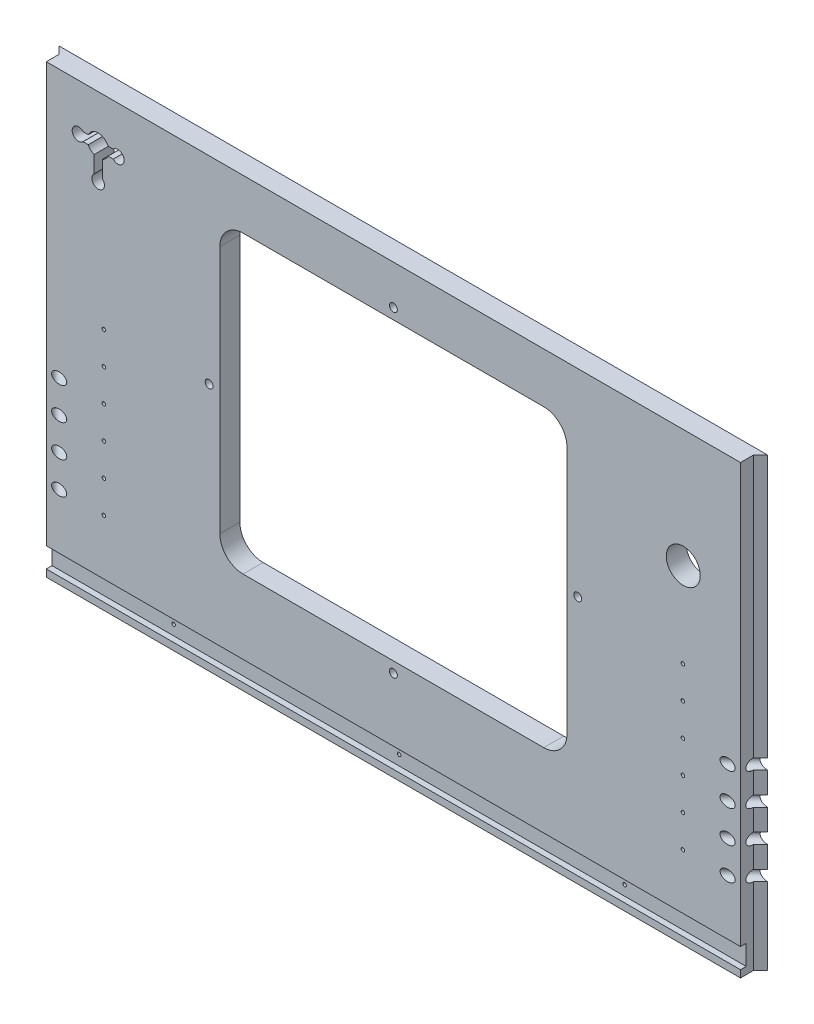
SolidWorks part; units mm, degrees
material "Maple"
ref_plane "Front Plane" through (0, 0, 0) normal (0, 0, 1) x (1, 0, 0)
ref_plane "Top Plane" through (0, 0, 0) normal (0, 1, 0) x (1, 0, 0)
ref_plane "Right Plane" through (0, 0, 0) normal (1, 0, 0) x (0, 0, -1)
sketch "Sketch1" plane through (0, 0, 0) normal (0, 0, 1) x (1, 0, 0)
  line L0 (8932.6508, -5243.5125) -> (10226.1458, -5243.5125)
  line L1 (9086.3208, -4722.0918) -> (10222.9708, -4853.7812)
  line L2 (8914.8708, -6342.0625) -> (10197.5708, -6342.0625)
  line L3 (8914.8708, -5808.6625) -> (10197.5708, -5808.6625)
  line L4 (8919.6333, -5253.0375) -> (10218.2083, -5253.0375)
  line L5 (9134.2633, -4656.1375) -> (9134.2633, -4638.3575)
  line L6 (9091.0833, -4638.3575) -> (9134.2633, -4638.3575)
  line L7 (9091.0833, -4567.2375) -> (9091.0833, -4638.3575)
  line L8 (9134.2633, -4656.1375) -> (9581.3033, -4656.1375)
  line L9 (9091.0833, -4567.2375) -> (9624.4833, -4567.2375)
  line L10 (9581.3033, -4656.1375) -> (9581.3033, -4638.3575)
  line L11 (9581.3033, -4638.3575) -> (9624.4833, -4638.3575)
  line L12 (9624.4833, -4567.2375) -> (9624.4833, -4638.3575)
  line L13 (8932.6508, -5225.7325) -> (9344.9775, -5225.7325)
  line L14 (8932.6508, -5256.2125) -> (8932.6508, -5243.5125)
  line L15 (8911.6958, -5256.2125) -> (8932.6508, -5256.2125)
  line L16 (8914.8708, -4722.0918) -> (9086.3208, -4722.0918)
  line L17 (8911.6958, -4715.5913) -> (8932.6508, -4715.5913)
  line L18 (8914.8708, -6342.0625) -> (8914.8708, -5808.6625)
  line L19 (12082.9917, -4722.0918) -> (10946.3417, -4853.7812)
  line L20 (12236.6617, -5243.5125) -> (10943.1667, -5243.5125)
  line L21 (10951.1042, -5253.0375) -> (12249.6792, -5253.0375)
  line L22 (10838.3917, -5656.2625) -> (11308.2917, -5656.2625)
  line L23 (10838.3917, -5719.7625) -> (11308.2917, -5719.7625)
  line L24 (10838.3917, -5742.5368) -> (11308.2917, -5742.5368)
  line L25 (10806.6417, -6342.0625) -> (11340.0417, -6342.0625)
  line L26 (10803.4667, -6335.7125) -> (11343.2167, -6335.7125)
  line L27 (10803.4667, -6317.9325) -> (11343.2167, -6317.9325)
  line L28 (10943.1667, -5225.7325) -> (11376.4483, -5225.7325)
  line L29 (11506.7292, -4754.5625) -> (10806.6417, -4827.5875)
  line L30 (11506.7292, -4567.2375) -> (11506.7292, -4754.5625)
  line L31 (10806.6417, -4567.2375) -> (10806.6417, -4827.5875)
  line L32 (10806.6417, -4567.2375) -> (11506.7292, -4567.2375)
  line L33 (10235.6708, -6329.3625) -> (10245.1958, -6329.3625)
  line L34 (10245.1958, -6329.3625) -> (10254.7208, -6278.5625)
  line L35 (10302.3458, -6329.3625) -> (10311.8708, -6278.5625)
  line L36 (10302.3458, -6329.3625) -> (10292.8208, -6329.3625)
  line L37 (10245.1958, -5821.3625) -> (10254.7208, -5872.1625)
  line L38 (10235.6708, -5821.3625) -> (10245.1958, -5821.3625)
  line L39 (10292.8208, -5821.3625) -> (10302.3458, -5821.3625)
  line L40 (10302.3458, -5821.3625) -> (10311.8708, -5872.1625)
  line L41 (10235.6708, -5821.3625) -> (10235.6708, -6329.3625)
  line L42 (10254.7208, -5872.1625) -> (10254.7208, -6278.5625)
  line L43 (10311.8708, -5872.1625) -> (10311.8708, -6278.5625)
  line L44 (10292.8208, -5821.3625) -> (10292.8208, -6329.3625)
  line L45 (8932.6508, -5225.7325) -> (8932.6508, -4715.5913)
  line L46 (8911.6958, -4715.5913) -> (8911.6958, -5256.2125)
  line L47 (8914.8708, -5248.275) -> (8914.8708, -4722.0918)
  line L48 (8919.6333, -5253.0375) -> (8914.8708, -5248.275)
  line L49 (8914.8708, -5145.0875) -> (8937.426, -5145.0875)
  line L50 (8914.8708, -5202.2375) -> (8937.426, -5202.2375)
  line L51 (10838.3917, -5656.2625) -> (10838.3917, -5719.7625)
  line L52 (10832.0417, -5736.1868) -> (10856.1717, -5736.1868)
  line L53 (10806.6417, -6342.0625) -> (10806.6417, -5818.7368)
  line L54 (10832.0417, -5649.9125) -> (10856.1717, -5649.9125)
  line L55 (10832.0417, -5726.1125) -> (10856.1717, -5726.1125)
  line L56 (10806.6417, -5818.7368) -> (10833.9015, -5818.7368)
  line L57 (10832.0417, -5806.0442) -> (10851.6815, -5806.0442)
  line L58 (10856.1717, -5801.5541) -> (10856.1717, -5736.1868)
  line L59 (10838.3917, -5814.2467) -> (10838.3917, -5742.5368)
  line L60 (10832.0417, -5806.0442) -> (10832.0417, -5736.1868)
  line L61 (10803.4667, -6317.9325) -> (10803.4667, -6335.7125)
  line L62 (10197.5708, -5808.6625) -> (10197.5708, -6342.0625)
  line L63 (9762.3842, -6348.4125) -> (9762.3842, -5802.3125)
  line L64 (9780.1642, -6348.4125) -> (9762.3842, -6348.4125)
  line L65 (9780.1642, -5802.3125) -> (9780.1642, -6348.4125)
  line L66 (9762.3842, -5802.3125) -> (9780.1642, -5802.3125)
  line L67 (9332.2775, -6348.4125) -> (9332.2775, -5802.3125)
  line L68 (9332.2775, -6348.4125) -> (9350.0575, -6348.4125)
  line L69 (9350.0575, -5802.3125) -> (9350.0575, -6348.4125)
  line L70 (9332.2775, -5802.3125) -> (9350.0575, -5802.3125)
  line L71 (9993.8374, -6061.075) -> (9993.8374, -6045.2418)
  line L72 (9998.5999, -6065.8375) -> (10014.4331, -6065.8375)
  line L73 (9998.5999, -6084.8875) -> (10014.4331, -6084.8875)
  line L74 (9993.8374, -6105.4832) -> (9993.8374, -6089.65)
  line L75 (9974.7874, -6105.4832) -> (9974.7874, -6089.65)
  line L76 (9954.1917, -6084.8875) -> (9970.0249, -6084.8875)
  line L77 (9974.7874, -6061.075) -> (9974.7874, -6045.2418)
  line L78 (9954.1917, -6065.8375) -> (9970.0249, -6065.8375)
  line L79 (10793.9417, -6237.2875) -> (10816.4969, -6237.2875)
  line L80 (10793.9417, -6294.4375) -> (10816.4969, -6294.4375)
  line L81 (10856.1717, -5649.9125) -> (10856.1717, -5726.1125)
  line L82 (10832.0417, -5726.1125) -> (10832.0417, -5649.9125)
  line L83 (10226.1458, -5225.7325) -> (10226.1458, -5243.5125)
  line L84 (10205.1908, -5257.8) -> (10205.1908, -4844.2499)
  line L85 (10230.9083, -4844.2499) -> (10230.9083, -5257.8)
  line L86 (10205.1908, -5257.8) -> (10230.9083, -5257.8)
  line L87 (10205.1908, -4844.2499) -> (10230.9083, -4844.2499)
  line L88 (10946.3417, -5176.8375) -> (10968.8969, -5176.8375)
  line L89 (9349.4676, -5141.9125) -> (9358.2674, -5141.9125)
  line L90 (10946.3417, -5119.6875) -> (10968.8969, -5119.6875)
  line L91 (9929.011, -4660.9635) -> (10066.0807, -4660.9635)
  line L92 (9929.011, -4678.7435) -> (10066.0807, -4678.7435)
  line L93 (10943.1667, -5225.7325) -> (10943.1667, -5243.5125)
  line L94 (10946.3417, -5248.275) -> (10951.1042, -5253.0375)
  line L95 (10946.3417, -5257.8063) -> (10946.3417, -4849.0188)
  line L96 (10964.1217, -5257.8) -> (10964.1217, -4844.2499)
  line L97 (10938.4042, -4844.2499) -> (10938.4042, -5257.8)
  line L98 (10938.4042, -5257.8) -> (10964.1217, -5257.8)
  line L99 (10964.1217, -4844.2499) -> (10938.4042, -4844.2499)
  line L100 (10344.8908, -4560.8875) -> (10369.0208, -4560.8875)
  line L101 (10344.8908, -4560.8875) -> (10369.0208, -4560.8875)
  line L102 (10800.2917, -4560.8875) -> (10824.4217, -4560.8875)
  line L103 (10200.4156, -5119.6875) -> (10222.9708, -5119.6875)
  line L104 (10200.4156, -5176.8375) -> (10222.9708, -5176.8375)
  line L105 (9344.9775, -5146.4026) -> (9344.9775, -5225.7325)
  line L106 (10344.8908, -4560.8875) -> (10344.8908, -4833.9375)
  line L107 (9792.8642, -5225.7325) -> (9792.8642, -5146.4026)
  line L108 (9362.7575, -5225.7325) -> (9775.0842, -5225.7325)
  line L109 (9680.3633, -4761.8396) -> (9680.3633, -4559.9604)
  line L110 (9656.2333, -4559.9604) -> (9680.3633, -4559.9604)
  line L111 (9656.2333, -4761.8396) -> (9680.3633, -4761.8396)
  line L112 (9656.2333, -4761.8396) -> (9656.2333, -4559.9604)
  line L113 (9779.5743, -5141.9125) -> (9788.374, -5141.9125)
  line L114 (10070.5708, -4665.4536) -> (10070.5708, -4674.2534)
  line L115 (9924.5208, -4674.2534) -> (9924.5208, -4665.4536)
  line L116 (12127.4417, -6188.3925) -> (12205.5015, -6188.3925)
  line L117 (12209.9917, -6170.6125) -> (12209.9917, -6183.9024)
  line L118 (9792.8642, -5225.7325) -> (10226.1458, -5225.7325)
  line L119 (9662.5833, -4754.5625) -> (10362.6708, -4827.5875)
  line L120 (9662.5833, -4567.2375) -> (9662.5833, -4754.5625)
  line L121 (10362.6708, -4567.2375) -> (10362.6708, -4827.5875)
  line L122 (9662.5833, -4567.2375) -> (10362.6708, -4567.2375)
  line L123 (10824.4217, -4833.9375) -> (10800.2917, -4833.9375)
  line L124 (10800.2917, -4833.9375) -> (10800.2917, -4560.8875)
  line L125 (10824.4217, -4560.8875) -> (10824.4217, -4833.9375)
  line L126 (10344.8908, -4833.9375) -> (10369.0208, -4833.9375)
  line L127 (10369.0208, -4833.9375) -> (10369.0208, -4560.8875)
  line L128 (10222.9708, -5248.275) -> (10218.2083, -5253.0375)
  line L129 (10222.9708, -5257.8063) -> (10222.9708, -4849.0188)
  line L130 (11734.6544, -5701.375) -> (11739.2301, -5701.375)
  line L131 (9362.7575, -5225.7325) -> (9362.7575, -5146.4026)
  line L132 (9775.0842, -5146.4026) -> (9775.0842, -5225.7325)
  line L133 (11761.3864, -5701.375) -> (11756.8282, -5701.375)
  line L134 (11734.6544, -5693.755) -> (11739.2301, -5693.755)
  line L135 (11761.4039, -5693.755) -> (11756.8282, -5693.755)
  line L136 (11734.6544, -5701.375) -> (11739.2301, -5701.375)
  line L137 (11744.3462, -5721.3024) -> (11744.3462, -5706.4179)
  line L138 (11751.7122, -5721.3024) -> (11751.7122, -5706.4179)
  line L139 (11740.0917, -6170.6125) -> (11740.0917, -6183.9024)
  line L140 (11689.2917, -6188.3925) -> (11822.6417, -6188.3925)
  line L141 (11689.2917, -6348.4093) -> (11689.2917, -6164.2657)
  line L142 (11689.2917, -6164.2657) -> (11746.4417, -6164.2657)
  line L143 (11746.4417, -6164.2657) -> (11746.4417, -6188.3925)
  line L144 (11689.2917, -6164.2657) -> (11746.4417, -6164.2657)
  line L145 (11340.0417, -5818.7368) -> (11340.0417, -6342.0625)
  line L146 (11290.5117, -5726.1125) -> (11314.6417, -5726.1125)
  line L147 (11290.5117, -5649.9125) -> (11290.5117, -5726.1125)
  line L148 (11340.0417, -5818.7368) -> (11312.7818, -5818.7368)
  line L149 (11314.6417, -5806.0442) -> (11295.0018, -5806.0442)
  line L150 (11290.5117, -5801.5541) -> (11290.5117, -5736.1868)
  line L151 (11308.2917, -5814.2467) -> (11308.2917, -5742.5368)
  line L152 (11314.6417, -5806.0442) -> (11314.6417, -5736.1868)
  line L153 (11290.5117, -5736.1868) -> (11314.6417, -5736.1868)
  line L154 (11848.0417, -6267.1325) -> (11962.3417, -6267.1325)
  line L155 (11962.3417, -6267.1325) -> (11962.3417, -6203.6325)
  line L156 (11343.2167, -6317.9325) -> (11343.2167, -6335.7125)
  line L157 (11365.4417, -5656.2625) -> (11365.4417, -5719.7625)
  line L158 (11365.4417, -5656.2625) -> (11479.7417, -5656.2625)
  line L159 (11778.1917, -6071.3937) -> (11802.3217, -6071.3937)
  line L160 (11314.6417, -5726.1125) -> (11314.6417, -5649.9125)
  line L161 (11314.6417, -5649.9125) -> (11290.5117, -5649.9125)
  line L162 (11308.2917, -5719.7625) -> (11308.2917, -5656.2625)
  line L163 (11689.2917, -6348.4093) -> (11713.4217, -6348.4093)
  line L164 (12203.6417, -6164.2657) -> (12260.7917, -6164.2657)
  line L165 (11713.4217, -6348.4093) -> (11713.4217, -6164.2657)
  line L166 (11695.6417, -6342.0625) -> (11695.6417, -6170.6125)
  line L167 (11695.6417, -6048.5337) -> (11699.4517, -6052.3437)
  line L168 (11822.6417, -6292.5325) -> (11822.6417, -6188.3925)
  line L169 (11695.6417, -6342.0625) -> (11695.6417, -6170.6125)
  line L170 (11848.0417, -6203.6325) -> (11962.3417, -6203.6325)
  line L171 (11848.0417, -6203.6325) -> (11848.0417, -6267.1325)
  line L172 (11987.7417, -6267.1325) -> (11987.7417, -6203.6325)
  line L173 (11784.5417, -6077.7437) -> (11784.5417, -6141.2438)
  line L174 (11517.8417, -5656.2625) -> (11632.1417, -5656.2625)
  line L175 (11632.1417, -5656.2625) -> (11632.1417, -5719.7625)
  line L176 (11632.1417, -5719.7625) -> (11517.8417, -5719.7625)
  line L177 (11517.8417, -5719.7625) -> (11517.8417, -5656.2625)
  line L178 (11692.4667, -6028.2137) -> (11692.4667, -6045.9937)
  line L179 (11695.6417, -5979.3188) -> (11718.1969, -5979.3188)
  line L180 (11695.6417, -5922.1687) -> (11718.1969, -5922.1687)
  line L181 (11821.0415, -5722.9375) -> (11821.0415, -5943.6)
  line L182 (11687.7042, -5651.5) -> (11701.9917, -5651.5)
  line L183 (11687.7042, -5651.5) -> (11687.7042, -6055.5251)
  line L184 (11687.7042, -6055.5251) -> (11701.9917, -6055.5251)
  line L185 (11701.9917, -6055.5251) -> (11701.9917, -5651.5)
  line L186 (11695.6417, -6055.2013) -> (11695.6417, -5649.595)
  line L187 (11695.6417, -5656.2625) -> (11695.6417, -6048.5337)
  line L188 (11695.6417, -6170.6125) -> (11740.0917, -6170.6125)
  line L189 (12203.6417, -6164.2657) -> (12203.6417, -6188.3925)
  line L190 (12254.4417, -6342.0625) -> (12254.4417, -6170.6125)
  line L191 (12129.0419, -5943.6) -> (12129.0419, -5722.9375)
  line L192 (12254.4417, -6048.5337) -> (12250.6317, -6052.3437)
  line L193 (12257.6167, -6045.9937) -> (12257.6167, -6028.2137)
  line L194 (12248.0917, -5651.5) -> (12262.3792, -5651.5)
  line L195 (12262.3792, -5651.5) -> (12262.3792, -6055.5251)
  line L196 (12262.3792, -6055.5251) -> (12248.0917, -6055.5251)
  line L197 (12248.0917, -6055.5251) -> (12248.0917, -5651.5)
  line L198 (12254.4417, -6141.2438) -> (12254.4417, -6077.7437)
  line L199 (12236.6617, -6164.2657) -> (12260.7917, -6164.2657)
  line L200 (12102.0417, -6267.1325) -> (11987.7417, -6267.1325)
  line L201 (11330.1865, -6237.2875) -> (11352.7417, -6237.2875)
  line L202 (11330.1865, -6294.4375) -> (11352.7417, -6294.4375)
  line L203 (11474.6617, -5851.8425) -> (11492.4417, -5851.8425)
  line L204 (11474.6617, -5808.6625) -> (11474.6617, -5851.8425)
  line L205 (11403.5417, -5808.6625) -> (11474.6617, -5808.6625)
  line L206 (11492.4417, -5851.8425) -> (11492.4417, -6298.8825)
  line L207 (11403.5417, -6342.0625) -> (11403.5417, -5808.6625)
  line L208 (11474.6617, -6298.8825) -> (11492.4417, -6298.8825)
  line L209 (11474.6617, -6342.0625) -> (11474.6617, -6298.8825)
  line L210 (11403.5417, -6342.0625) -> (11474.6617, -6342.0625)
  line L211 (11619.4417, -5851.8425) -> (11601.6617, -5851.8425)
  line L212 (11601.6617, -5808.6625) -> (11601.6617, -5851.8425)
  line L213 (11530.5417, -5808.6625) -> (11601.6617, -5808.6625)
  line L214 (11619.4417, -5851.8425) -> (11619.4417, -6298.8825)
  line L215 (11530.5417, -6342.0625) -> (11530.5417, -5808.6625)
  line L216 (11619.4417, -6298.8825) -> (11601.6617, -6298.8825)
  line L217 (11601.6617, -6342.0625) -> (11601.6617, -6298.8825)
  line L218 (11530.5417, -6342.0625) -> (11601.6617, -6342.0625)
  line L219 (11479.7417, -5719.7625) -> (11479.7417, -5656.2625)
  line L220 (11365.4417, -5719.7625) -> (11479.7417, -5719.7625)
  line L221 (11778.1917, -6147.5937) -> (11802.3217, -6147.5937)
  line L222 (11802.3217, -6071.3937) -> (11802.3217, -6147.5937)
  line L223 (11778.1917, -6147.5937) -> (11778.1917, -6071.3937)
  line L224 (12254.4417, -5922.1687) -> (12231.8865, -5922.1687)
  line L225 (12254.4417, -5979.3188) -> (12231.8865, -5979.3188)
  line L226 (12254.4417, -6055.2013) -> (12254.4417, -5649.595)
  line L227 (12254.4417, -6048.5337) -> (12254.4417, -5656.2625)
  line L228 (11841.6917, -5702.2873) -> (12108.3917, -5702.2873)
  line L229 (11822.6417, -6292.5325) -> (12127.4417, -6292.5325)
  line L230 (12127.4417, -6292.5325) -> (12127.4417, -6188.3925)
  line L231 (12254.4417, -6170.6125) -> (12209.9917, -6170.6125)
  line L232 (11695.6417, -6342.0625) -> (12254.4417, -6342.0625)
  line L233 (12236.6617, -6348.4093) -> (12260.7917, -6348.4093)
  line L234 (12260.7917, -6348.4093) -> (12260.7917, -6164.2657)
  line L235 (12236.6617, -6348.4093) -> (12236.6617, -6164.2657)
  line L236 (12102.0417, -6203.6325) -> (12102.0417, -6267.1325)
  line L237 (11987.7417, -6203.6325) -> (12102.0417, -6203.6325)
  line L238 (12236.6617, -6147.5937) -> (12236.6617, -6071.3937)
  line L239 (12203.6417, -6188.3925) -> (12260.7917, -6188.3925)
  line L240 (11098.7417, -4665.4536) -> (11098.7417, -4674.2534)
  line L241 (11394.2283, -5146.4026) -> (11394.2283, -5225.7325)
  line L242 (11376.4483, -5225.7325) -> (11376.4483, -5146.4026)
  line L243 (11394.2283, -5225.7325) -> (11806.555, -5225.7325)
  line L244 (11841.6917, -5964.2502) -> (12108.3917, -5964.2502)
  line L245 (12236.6617, -6147.5937) -> (12260.7917, -6147.5937)
  line L246 (12236.6617, -5256.2125) -> (12236.6617, -5243.5125)
  line L247 (12260.7917, -6147.5937) -> (12260.7917, -6071.3937)
  line L248 (12260.7917, -6071.3937) -> (12236.6617, -6071.3937)
  line L249 (12254.4417, -6077.7437) -> (11784.5417, -6077.7437)
  line L250 (11784.5417, -6141.2438) -> (12254.4417, -6141.2438)
  line L252 (12254.4417, -5656.2625) -> (11695.6417, -5656.2625)
  line L253 (11699.4517, -6052.3437) -> (12250.6317, -6052.3437)
  line L254 (11692.4667, -6045.9937) -> (12257.6167, -6045.9937)
  line L255 (11692.4667, -6028.2137) -> (12257.6167, -6028.2137)
  line L256 (11824.335, -5146.4026) -> (11824.335, -5225.7325)
  line L257 (11811.0451, -5141.9125) -> (11819.8449, -5141.9125)
  line L258 (11244.7917, -4674.2534) -> (11244.7917, -4665.4536)
  line L259 (11806.555, -5225.7325) -> (11806.555, -5146.4026)
  line L260 (11488.9492, -4761.8396) -> (11488.9492, -4559.9604)
  line L261 (11488.9492, -4559.9604) -> (11513.0792, -4559.9604)
  line L262 (11488.9492, -4761.8396) -> (11513.0792, -4761.8396)
  line L263 (11513.0792, -4761.8396) -> (11513.0792, -4559.9604)
  line L264 (11240.3015, -4660.9635) -> (11103.2318, -4660.9635)
  line L265 (11103.2318, -4678.7435) -> (11240.3015, -4678.7435)
  line L266 (12236.6617, -5225.7325) -> (12236.6617, -4715.5913)
  line L267 (12257.6167, -4715.5913) -> (12257.6167, -5256.2125)
  line L268 (12254.4417, -5248.275) -> (12254.4417, -4722.0918)
  line L269 (12236.6617, -5225.7325) -> (11824.335, -5225.7325)
  line L270 (12035.0492, -4656.1375) -> (12035.0492, -4638.3575)
  line L271 (12078.2292, -4638.3575) -> (12035.0492, -4638.3575)
  line L272 (12078.2292, -4567.2375) -> (12078.2292, -4638.3575)
  line L273 (12035.0492, -4656.1375) -> (11588.0092, -4656.1375)
  line L274 (11544.8292, -4567.2375) -> (12078.2292, -4567.2375)
  line L275 (11588.0092, -4656.1375) -> (11588.0092, -4638.3575)
  line L276 (11544.8292, -4638.3575) -> (11588.0092, -4638.3575)
  line L277 (11544.8292, -4567.2375) -> (11544.8292, -4638.3575)
  line L278 (12249.6792, -5253.0375) -> (12254.4417, -5248.275)
  line L280 (12257.6167, -5256.2125) -> (12236.6617, -5256.2125)
  line L281 (12231.8865, -5145.0875) -> (12254.4417, -5145.0875)
  line L282 (12231.8865, -5202.2375) -> (12254.4417, -5202.2375)
  line L283 (12236.6617, -4715.5913) -> (12257.6167, -4715.5913)
  line L284 (12082.9917, -4722.0918) -> (12254.4417, -4722.0918)
  line L285 (11380.9385, -5141.9125) -> (11389.7382, -5141.9125)
  circle A0 centre (8923.7608, -4778.9042) radius 1.5875
  circle A1 centre (9062.6598, -4736.3765) radius 2.3685
  circle A2 centre (9051.3958, -6281.7375) radius 22.225
  circle A3 centre (9083.1458, -6249.9875) radius 1.5875
  circle A4 centre (9083.1458, -6313.4875) radius 1.5875
  circle A5 centre (9019.6458, -6249.9875) radius 1.5875
  circle A6 centre (9019.6458, -6313.4875) radius 1.5875
  circle A7 centre (8972.3383, -5202.2375) radius 1.5875
  circle A8 centre (8923.7608, -5015.9708) radius 1.5875
  circle A9 centre (8923.7608, -5134.5042) radius 1.5875
  circle A10 centre (9054.5708, -5234.6225) radius 1.5875
  circle A11 centre (8923.7608, -4897.4375) radius 1.5875
  circle A12 centre (8972.3383, -5087.9375) radius 1.5875
  circle A13 centre (8972.3383, -5145.0875) radius 1.5875
  circle A14 centre (10847.2817, -5668.9625) radius 1.5875
  circle A15 centre (10847.2817, -5707.0625) radius 1.5875
  circle A16 centre (10847.2817, -5755.2368) radius 1.5875
  circle A17 centre (10851.4092, -6237.2875) radius 1.5875
  circle A18 centre (10851.4092, -6294.4375) radius 1.5875
  circle A19 centre (10847.2817, -5793.3442) radius 1.5875
  arc A20 (10833.9015, -5818.7368) -> (10838.3917, -5814.2467) centre (10836.1466, -5816.4918) ccw
  arc A21 (10851.6815, -5806.0442) -> (10856.1717, -5801.5541) centre (10853.9266, -5803.7992) ccw
  circle A22 centre (10882.8417, -6040.4375) radius 1.5875
  circle A23 centre (10882.8417, -6218.2375) radius 1.5875
  circle A24 centre (10882.8417, -5862.6375) radius 1.5875
  circle A25 centre (10908.2417, -6326.8225) radius 1.5875
  circle A26 centre (10908.2417, -6326.8225) radius 1.5875
  circle A27 centre (10851.4092, -6180.1375) radius 1.5875
  circle A28 centre (10815.5317, -4783.4231) radius 1.5875
  circle A29 centre (10815.5317, -4696.9488) radius 1.5875
  circle A30 centre (10815.5317, -4610.4746) radius 1.5875
  circle A31 centre (10979.1323, -4867.0082) radius 2.3685
  circle A32 centre (10190.1802, -4867.0082) radius 2.3685
  circle A33 centre (10955.2317, -4929.9812) radius 1.5875
  circle A34 centre (10955.2317, -5031.5812) radius 1.5875
  circle A35 centre (10214.0808, -4929.9812) radius 1.5875
  circle A36 centre (10214.0808, -5031.5812) radius 1.5875
  circle A37 centre (9341.1675, -6265.8625) radius 1.5875
  circle A38 centre (9771.2742, -5884.8625) radius 1.5875
  circle A39 centre (9771.2742, -6138.8625) radius 1.5875
  circle A40 centre (9771.2742, -6011.8625) radius 1.5875
  arc A41 (10036.2287, -6113.8083) -> (10051.3426, -6111.6033) centre (10042.9639, -6107.0732) ccw
  arc A42 (10051.3426, -6111.6033) -> (10051.3426, -6039.1217) centre (9984.3124, -6075.3625) ccw
  arc A43 (10051.3426, -6039.1217) -> (10036.2287, -6036.9167) centre (10042.9639, -6043.6518) ccw
  arc A44 (10034.5851, -6102.5431) -> (10034.5851, -6048.1819) centre (9984.3124, -6075.3625) ccw
  arc A45 (10034.5851, -6102.5431) -> (10036.2287, -6113.8083) centre (10042.9639, -6107.0732) ccw
  arc A46 (10036.2287, -6036.9167) -> (10034.5851, -6048.1819) centre (10042.9639, -6043.6518) ccw
  arc A47 (9945.8666, -6127.2787) -> (9948.0717, -6142.3927) centre (9952.6018, -6134.0139) ccw
  arc A48 (9948.0717, -6142.3927) -> (10020.5532, -6142.3927) centre (9984.3124, -6075.3625) ccw
  arc A49 (10020.5532, -6142.3927) -> (10022.7583, -6127.2787) centre (10016.0231, -6134.0139) ccw
  arc A50 (9957.1319, -6125.6352) -> (10011.493, -6125.6352) centre (9984.3124, -6075.3625) ccw
  arc A51 (9957.1319, -6125.6352) -> (9945.8666, -6127.2787) centre (9952.6018, -6134.0139) ccw
  arc A52 (10022.7583, -6127.2787) -> (10011.493, -6125.6352) centre (10016.0231, -6134.0139) ccw
  arc A53 (9932.3962, -6036.9167) -> (9917.2822, -6039.1217) centre (9925.661, -6043.6518) ccw
  arc A54 (9917.2822, -6039.1217) -> (9917.2822, -6111.6033) centre (9984.3124, -6075.3625) ccw
  arc A55 (9917.2822, -6111.6033) -> (9932.3962, -6113.8083) centre (9925.661, -6107.0732) ccw
  arc A56 (9934.0398, -6048.1819) -> (9934.0398, -6102.5431) centre (9984.3124, -6075.3625) ccw
  arc A57 (9934.0398, -6048.1819) -> (9932.3962, -6036.9167) centre (9925.661, -6043.6518) ccw
  arc A58 (9932.3962, -6113.8083) -> (9934.0398, -6102.5431) centre (9925.661, -6107.0732) ccw
  arc A59 (9945.8666, -6023.4463) -> (9957.1319, -6025.0898) centre (9952.6018, -6016.7111) ccw
  arc A60 (10011.493, -6025.0898) -> (10022.7583, -6023.4463) centre (10016.0231, -6016.7111) ccw
  arc A61 (10011.493, -6025.0898) -> (9957.1319, -6025.0898) centre (9984.3124, -6075.3625) ccw
  arc A62 (9948.0717, -6008.3323) -> (9945.8666, -6023.4463) centre (9952.6018, -6016.7111) ccw
  arc A63 (10020.5532, -6008.3323) -> (9948.0717, -6008.3323) centre (9984.3124, -6075.3625) ccw
  arc A64 (10022.7583, -6023.4463) -> (10020.5532, -6008.3323) centre (10016.0231, -6016.7111) ccw
  arc A65 (10005.0943, -6187.7574) -> (10096.7073, -6096.1443) centre (9984.3124, -6075.3625) ccw
  arc A66 (9993.8374, -6178.3911) -> (10005.0943, -6187.7574) centre (10003.3624, -6178.3911) ccw
  arc A67 (10001.6306, -6169.0249) -> (10077.9748, -6092.6807) centre (9984.3124, -6075.3625) ccw
  arc A68 (10087.3411, -6084.8875) -> (10077.9748, -6092.6807) centre (10087.3411, -6094.4125) ccw
  arc A69 (10001.6306, -6169.0249) -> (9993.8374, -6178.3911) centre (10003.3624, -6178.3911) ccw
  arc A70 (9963.5306, -6187.7574) -> (9974.7874, -6178.3911) centre (9965.2624, -6178.3911) ccw
  arc A71 (9871.9176, -6096.1443) -> (9963.5306, -6187.7574) centre (9984.3124, -6075.3625) ccw
  arc A72 (9881.2838, -6084.8875) -> (9871.9176, -6096.1443) centre (9881.2838, -6094.4125) ccw
  arc A73 (9890.65, -6092.6807) -> (9966.9943, -6169.0249) centre (9984.3124, -6075.3625) ccw
  arc A74 (9974.7874, -6178.3911) -> (9966.9943, -6169.0249) centre (9965.2624, -6178.3911) ccw
  arc A75 (9890.65, -6092.6807) -> (9881.2838, -6084.8875) centre (9881.2838, -6094.4125) ccw
  arc A76 (9871.9176, -6054.5807) -> (9881.2838, -6065.8375) centre (9881.2838, -6056.3125) ccw
  arc A77 (9963.5306, -5962.9676) -> (9871.9176, -6054.5807) centre (9984.3124, -6075.3625) ccw
  arc A78 (9974.7874, -5972.3339) -> (9963.5306, -5962.9676) centre (9965.2624, -5972.3339) ccw
  arc A79 (9966.9943, -5981.7001) -> (9890.65, -6058.0443) centre (9984.3124, -6075.3625) ccw
  arc A80 (9881.2838, -6065.8375) -> (9890.65, -6058.0443) centre (9881.2838, -6056.3125) ccw
  arc A81 (9966.9943, -5981.7001) -> (9974.7874, -5972.3339) centre (9965.2624, -5972.3339) ccw
  arc A82 (10077.9748, -6058.0443) -> (10087.3411, -6065.8375) centre (10087.3411, -6056.3125) ccw
  arc A83 (9993.8374, -5972.3339) -> (10001.6306, -5981.7001) centre (10003.3624, -5972.3339) ccw
  arc A84 (10077.9748, -6058.0443) -> (10001.6306, -5981.7001) centre (9984.3124, -6075.3625) ccw
  arc A85 (10087.3411, -6065.8375) -> (10096.7073, -6054.5807) centre (10087.3411, -6056.3125) ccw
  arc A86 (10096.7073, -6054.5807) -> (10005.0943, -5962.9676) centre (9984.3124, -6075.3625) ccw
  arc A87 (10005.0943, -5962.9676) -> (9993.8374, -5972.3339) centre (10003.3624, -5972.3339) ccw
  arc A88 (10014.4331, -6065.8375) -> (10018.7361, -6059.0339) centre (10014.4331, -6061.075) ccw
  arc A89 (10018.7361, -6059.0339) -> (10000.641, -6040.9388) centre (9984.3124, -6075.3625) ccw
  arc A90 (10000.641, -6040.9388) -> (9993.8374, -6045.2418) centre (9998.5999, -6045.2418) ccw
  arc A91 (9993.8374, -6061.075) -> (9998.5999, -6065.8375) centre (9998.5999, -6061.075) ccw
  arc A92 (9993.8374, -6105.4832) -> (10000.641, -6109.7862) centre (9998.5999, -6105.4832) ccw
  arc A93 (10000.641, -6109.7862) -> (10018.7361, -6091.6911) centre (9984.3124, -6075.3625) ccw
  arc A94 (10018.7361, -6091.6911) -> (10014.4331, -6084.8875) centre (10014.4331, -6089.65) ccw
  arc A95 (9998.5999, -6084.8875) -> (9993.8374, -6089.65) centre (9998.5999, -6089.65) ccw
  arc A96 (9954.1917, -6084.8875) -> (9949.8888, -6091.6911) centre (9954.1917, -6089.65) ccw
  arc A97 (9949.8888, -6091.6911) -> (9967.9839, -6109.7862) centre (9984.3124, -6075.3625) ccw
  arc A98 (9967.9839, -6109.7862) -> (9974.7874, -6105.4832) centre (9970.0249, -6105.4832) ccw
  arc A99 (9974.7874, -6089.65) -> (9970.0249, -6084.8875) centre (9970.0249, -6089.65) ccw
  arc A100 (9970.0249, -6065.8375) -> (9974.7874, -6061.075) centre (9970.0249, -6061.075) ccw
  arc A101 (9949.8888, -6059.0339) -> (9954.1917, -6065.8375) centre (9954.1917, -6061.075) ccw
  arc A102 (9967.9839, -6040.9388) -> (9949.8888, -6059.0339) centre (9984.3124, -6075.3625) ccw
  arc A103 (9974.7874, -6045.2418) -> (9967.9839, -6040.9388) centre (9970.0249, -6045.2418) ccw
  arc A104 (10096.7073, -6096.1443) -> (10087.3411, -6084.8875) centre (10087.3411, -6094.4125) ccw
  circle A105 centre (9771.2742, -6265.8625) radius 1.5875
  circle A106 centre (9341.1675, -5884.8625) radius 1.5875
  circle A107 centre (9341.1675, -6138.8625) radius 1.5875
  circle A108 centre (9341.1675, -6011.8625) radius 1.5875
  circle A109 centre (11037.2315, -4887.5494) radius 15.0812
  arc A110 (9349.4676, -5141.9125) -> (9344.9775, -5146.4026) centre (9347.2226, -5144.1576) ccw
  arc A111 (9362.7575, -5146.4026) -> (9358.2674, -5141.9125) centre (9360.5124, -5144.1576) ccw
  circle A112 centre (9946.7458, -4669.8535) radius 1.5875
  arc A113 (9924.5208, -4674.2534) -> (9929.011, -4678.7435) centre (9926.7659, -4676.4984) ccw
  circle A114 centre (11003.8092, -5176.8375) radius 1.5875
  circle A115 centre (11003.8092, -5119.6875) radius 1.5875
  circle A116 centre (10353.7808, -4696.9488) radius 1.5875
  circle A117 centre (10353.7808, -4610.4746) radius 1.5875
  circle A118 centre (10353.7808, -4783.4231) radius 1.5875
  circle A119 centre (11003.8092, -5062.5375) radius 1.5875
  circle A120 centre (9353.8675, -5160.9625) radius 1.5875
  circle A121 centre (9638.7708, -5234.6225) radius 1.5875
  circle A122 centre (9671.4733, -4724.1144) radius 1.5875
  circle A123 centre (9671.4733, -4661.3637) radius 1.5875
  circle A124 centre (9671.4733, -4598.6129) radius 1.5875
  arc A125 (9792.8642, -5146.4026) -> (9788.374, -5141.9125) centre (9790.6191, -5144.1576) ccw
  arc A126 (9779.5743, -5141.9125) -> (9775.0842, -5146.4026) centre (9777.3292, -5144.1576) ccw
  circle A127 centre (10048.3458, -4669.8535) radius 1.5875
  arc A128 (10070.5708, -4665.4536) -> (10066.0807, -4660.9635) centre (10068.3258, -4663.2086) ccw
  arc A129 (10066.0807, -4678.7435) -> (10070.5708, -4674.2534) centre (10068.3258, -4676.4984) ccw
  circle A130 centre (9997.5458, -4669.8535) radius 1.5875
  arc A131 (9929.011, -4660.9635) -> (9924.5208, -4665.4536) centre (9926.7659, -4663.2086) ccw
  circle A132 centre (10132.081, -4887.5494) radius 15.0812
  circle A133 centre (10165.5033, -5176.8375) radius 1.5875
  circle A134 centre (10165.5033, -5119.6875) radius 1.5875
  circle A135 centre (9486.3708, -5234.6225) radius 1.5875
  circle A136 centre (10165.5033, -5062.5375) radius 1.5875
  circle A137 centre (9206.9708, -5234.6225) radius 1.5875
  circle A138 centre (10070.5708, -5234.6225) radius 1.5875
  circle A139 centre (9918.1708, -5234.6225) radius 1.5875
  circle A140 centre (9783.9742, -5160.9625) radius 1.5875
  circle A141 centre (9783.9742, -5193.9825) radius 1.5875
  circle A142 centre (9353.8675, -5193.9825) radius 1.5875
  circle A143 centre (11073.3417, -6326.8225) radius 1.5875
  circle A144 centre (11073.3417, -6326.8225) radius 1.5875
  circle A145 centre (11295.2742, -6180.1375) radius 1.5875
  circle A146 centre (11295.2742, -6294.4375) radius 1.5875
  circle A147 centre (11295.2742, -6237.2875) radius 1.5875
  circle A148 centre (11975.0417, -5692.775) radius 3.4925
  circle A149 centre (11263.8417, -5862.6375) radius 1.5875
  arc A150 (11739.2301, -5701.375) -> (11744.3462, -5706.4179) centre (11748.0292, -5697.565) ccw
  arc A151 (11751.7122, -5706.4179) -> (11756.8282, -5701.375) centre (11748.0292, -5697.565) ccw
  arc A152 (11744.3462, -5721.3024) -> (11751.7122, -5721.3024) centre (11748.0292, -5725.505) ccw
  arc A153 (11734.6544, -5693.755) -> (11724.9787, -5697.565) centre (11730.5667, -5697.565) ccw
  arc A154 (11756.8282, -5693.755) -> (11739.2301, -5693.755) centre (11748.0292, -5697.565) ccw
  arc A155 (11724.9787, -5697.565) -> (11734.6544, -5701.375) centre (11730.5667, -5697.565) ccw
  arc A156 (11761.3864, -5701.375) -> (11771.0797, -5697.565) centre (11765.4842, -5697.565) ccw
  arc A157 (11771.0797, -5697.565) -> (11761.4039, -5693.755) centre (11765.4917, -5697.565) ccw
  arc A158 (11740.0917, -6183.9024) -> (11744.5818, -6188.3925) centre (11742.3367, -6186.1474) ccw
  arc A159 (12205.5015, -6188.3925) -> (12209.9917, -6183.9024) centre (12207.7466, -6186.1474) ccw
  circle A160 centre (11299.4017, -5793.3442) radius 1.5875
  arc A161 (11308.2917, -5814.2467) -> (11312.7818, -5818.7368) centre (11310.5367, -5816.4918) ccw
  arc A162 (11290.5117, -5801.5541) -> (11295.0018, -5806.0442) centre (11292.7567, -5803.7992) ccw
  circle A163 centre (11704.5317, -6314.149) radius 1.5875
  circle A164 centre (11748.9817, -6208.7125) radius 1.5875
  circle A165 centre (11263.8417, -6218.2375) radius 1.5875
  circle A166 centre (11263.8417, -6040.4375) radius 1.5875
  circle A167 centre (11238.4417, -6326.8225) radius 1.5875
  circle A168 centre (11238.4417, -6326.8225) radius 1.5875
  circle A169 centre (11299.4017, -5668.9625) radius 1.5875
  circle A170 centre (11299.4017, -5707.0625) radius 1.5875
  circle A171 centre (11726.7567, -6179.5025) radius 1.5875
  circle A172 centre (11704.5317, -6199.3198) radius 1.5875
  circle A173 centre (11748.9817, -6272.2125) radius 1.5875
  circle A174 centre (11704.5317, -6256.7344) radius 1.5875
  circle A175 centre (11299.4017, -5755.2368) radius 1.5875
  circle A176 centre (11913.4467, -6301.4225) radius 1.5875
  circle A177 centre (11790.2567, -6301.4225) radius 1.5875
  circle A178 centre (11793.4317, -6128.5437) radius 1.5875
  circle A179 centre (11753.1092, -5865.0188) radius 1.5875
  circle A180 centre (11809.9417, -6037.1038) radius 1.5875
  circle A181 centre (11809.9417, -6037.1038) radius 1.5875
  circle A182 centre (11753.1092, -5922.1687) radius 1.5875
  circle A183 centre (11975.0417, -5973.7625) radius 3.4925
  circle A184 centre (11975.0417, -6037.1038) radius 1.5875
  circle A185 centre (11753.1092, -5979.3188) radius 1.5875
  circle A186 centre (11975.0417, -6037.1038) radius 1.5875
  arc A187 (11841.6917, -5702.2873) -> (11821.0415, -5722.9375) centre (11841.6917, -5722.9375) ccw
  circle A188 centre (11811.5292, -5833.2687) radius 3.4925
  arc A189 (11821.0415, -5943.6) -> (11841.6917, -5964.2502) centre (11841.6917, -5943.6) ccw
  circle A190 centre (12196.9742, -5865.0188) radius 1.5875
  arc A191 (12129.0419, -5722.9375) -> (12108.3917, -5702.2873) centre (12108.3917, -5722.9375) ccw
  circle A192 centre (12036.6367, -6301.4225) radius 1.5875
  circle A193 centre (12159.8267, -6301.4225) radius 1.5875
  circle A194 centre (12138.5542, -5833.2687) radius 3.4925
  circle A195 centre (12197.2917, -5761.0375) radius 15.0812
  circle A196 centre (11793.4317, -6090.4437) radius 1.5875
  circle A197 centre (12196.9742, -5922.1687) radius 1.5875
  arc A198 (12108.3917, -5964.2502) -> (12129.0419, -5943.6) centre (12108.3917, -5943.6) ccw
  circle A199 centre (12196.9742, -5979.3188) radius 1.5875
  circle A200 centre (12201.1017, -6272.2125) radius 1.5875
  circle A201 centre (12245.5517, -6314.149) radius 1.5875
  circle A202 centre (12245.5517, -6256.7344) radius 1.5875
  circle A203 centre (12201.1017, -6208.7125) radius 1.5875
  circle A204 centre (12223.3267, -6179.5025) radius 1.5875
  circle A205 centre (12245.5517, -6199.3198) radius 1.5875
  circle A206 centre (11171.7667, -4669.8535) radius 1.5875
  circle A207 centre (11222.5667, -4669.8535) radius 1.5875
  arc A208 (11240.3015, -4678.7435) -> (11244.7917, -4674.2534) centre (11242.5466, -4676.4984) ccw
  circle A209 centre (11385.3383, -5193.9825) radius 1.5875
  circle A210 centre (12106.6527, -4736.3765) radius 2.3685
  circle A211 centre (12140.1417, -6037.1038) radius 1.5875
  circle A212 centre (12140.1417, -6037.1038) radius 1.5875
  circle A213 centre (12245.5517, -6090.4437) radius 1.5875
  circle A214 centre (12245.5517, -6128.5437) radius 1.5875
  circle A215 centre (11385.3383, -5160.9625) radius 1.5875
  arc A216 (11824.335, -5146.4026) -> (11819.8449, -5141.9125) centre (11822.0899, -5144.1576) ccw
  arc A217 (11811.0451, -5141.9125) -> (11806.555, -5146.4026) centre (11808.8001, -5144.1576) ccw
  circle A218 centre (11815.445, -5193.9825) radius 1.5875
  circle A219 centre (11815.445, -5160.9625) radius 1.5875
  circle A220 centre (11530.5417, -5234.6225) radius 1.5875
  circle A221 centre (11962.3417, -5234.6225) radius 1.5875
  arc A222 (11244.7917, -4665.4536) -> (11240.3015, -4660.9635) centre (11242.5466, -4663.2086) ccw
  circle A223 centre (11682.9417, -5234.6225) radius 1.5875
  circle A224 centre (11497.8392, -4724.1144) radius 1.5875
  circle A225 centre (11497.8392, -4661.3637) radius 1.5875
  circle A226 centre (11497.8392, -4598.6129) radius 1.5875
  circle A227 centre (11120.9667, -4669.8535) radius 1.5875
  arc A228 (11103.2318, -4660.9635) -> (11098.7417, -4665.4536) centre (11100.9867, -4663.2086) ccw
  arc A229 (11098.7417, -4674.2534) -> (11103.2318, -4678.7435) centre (11100.9867, -4676.4984) ccw
  circle A230 centre (12196.9742, -5202.2375) radius 1.5875
  circle A231 centre (12245.5517, -5015.9708) radius 1.5875
  circle A232 centre (12245.5517, -5134.5042) radius 1.5875
  circle A233 centre (12114.7417, -5234.6225) radius 1.5875
  circle A234 centre (12245.5517, -4897.4375) radius 1.5875
  circle A235 centre (12245.5517, -4778.9042) radius 1.5875
  circle A236 centre (12196.9742, -5087.9375) radius 1.5875
  circle A237 centre (12196.9742, -5145.0875) radius 1.5875
  circle A238 centre (11098.7417, -5234.6225) radius 1.5875
  circle A239 centre (11251.1417, -5234.6225) radius 1.5875
  arc A240 (11380.9385, -5141.9125) -> (11376.4483, -5146.4026) centre (11378.6934, -5144.1576) ccw
  arc A241 (11394.2283, -5146.4026) -> (11389.7382, -5141.9125) centre (11391.9833, -5144.1576) ccw
sketch "CabFrontOutline" plane through (0, 0, 0) normal (0, 0, 1) x (1, 0, 0)
  line L0 (11695.6417, -6055.2013) -> (11695.6417, -5649.595) construction
  line L1 (11695.6417, -6052.3437) -> (12324.2917, -6052.3437)
  line L3 (12324.2917, -6052.3437) -> (12324.2917, -5656.2625)
  line L4 (12324.2917, -5656.2625) -> (11695.6417, -5656.2625)
  line L5 (11695.6417, -5656.2625) -> (11695.6417, -6052.3437)
  point P1 (0, 0)
  point P2 (0, 0)
  dimension "CabFrontWidth" = 628.65
extrude "CabFront_Thickness" add sketch "CabFrontOutline" against normal blind 17.78
sketch "CabFront_CoinDoorCuts" plane through (0, 0, 0) normal (0, 0, 1) x (1, 0, 0)
  line L10 (11753.1092, -5865.0188) -> (11753.1092, -5922.1687) construction
  line L11 (11753.1092, -5922.1687) -> (11753.1092, -5979.3188) construction
  line L12 (11695.6417, -5656.2625) -> (11695.6417, -6052.3437) construction
  line L13 (12266.8242, -5865.0188) -> (12266.8242, -5922.1687) construction
  line L14 (12266.8242, -5922.1687) -> (12266.8242, -5979.3188) construction
  line L15 (12324.2917, -6052.3437) -> (12324.2917, -5656.2625) construction
  line L16 (11809.9417, -6037.1038) -> (12009.9667, -6037.1038) construction
  line L17 (12009.9667, -6037.1038) -> (12209.9917, -6037.1038) construction
  line L18 (12009.9667, -6037.1038) -> (12009.9667, -6052.3437) construction
  line L19 (11695.6417, -6052.3437) -> (12324.2917, -6052.3437) construction
  circle A0 centre (11753.1092, -5893.5938) radius 1.5875
  circle A1 centre (11753.1092, -5950.7437) radius 1.5875
  circle A2 centre (12266.8242, -5893.5938) radius 1.5875
  circle A3 centre (12266.8242, -5950.7437) radius 1.5875
  circle A4 centre (11753.1092, -5836.4438) radius 1.5875
  circle A15 centre (12266.8242, -5836.4438) radius 1.5875
  circle A20 centre (12266.8242, -5865.0188) radius 1.5875
  circle A21 centre (12266.8242, -5922.1687) radius 1.5875
  circle A22 centre (12266.8242, -5979.3188) radius 1.5875
  circle A23 centre (12209.9917, -6037.1038) radius 1.5875
  circle A24 centre (12009.9667, -6037.1038) radius 1.5875
  circle A25 centre (11809.9417, -6037.1038) radius 1.5875
  circle A26 centre (11753.1092, -5979.3188) radius 1.5875
  circle A27 centre (11753.1092, -5922.1687) radius 1.5875
  circle A28 centre (11753.1092, -5865.0188) radius 1.5875
  dimension "D1" = 57.4675
  dimension "D2" = 57.4675
extrude "Cut-Extrude1" cut sketch "CabFront_CoinDoorCuts" against normal blind 12.7
sketch "Sketch5" plane through (0, 0, 0) normal (0, 0, 1) x (1, 0, 0)
  line L0 (11855.9665, -5700.6998) -> (12163.9669, -5700.6998)
  line L1 (12163.9669, -5700.6998) -> (12163.9669, -5962.6627)
  line L2 (12163.9669, -5962.6627) -> (11855.9665, -5962.6627)
  line L3 (11855.9665, -5962.6627) -> (11855.9665, -5700.6998)
  line L4 (11734.6544, -5693.755) -> (11739.2301, -5693.755)
  line L5 (11734.6544, -5701.375) -> (11739.2301, -5701.375)
  line L6 (11744.3462, -5706.4179) -> (11744.3462, -5721.3024)
  line L7 (11751.7122, -5706.4179) -> (11751.7122, -5721.3024)
  line L8 (11756.8282, -5701.375) -> (11761.3864, -5701.375)
  line L9 (11761.3864, -5693.755) -> (11756.8282, -5693.755)
  line L20 (12009.9667, -5691.1875) -> (12009.9667, -5700.6998) construction
  line L21 (11846.4542, -5831.6812) -> (11855.9665, -5831.6812) construction
  line L22 (12009.9667, -5972.175) -> (12009.9667, -5962.6627) construction
  line L23 (12173.4792, -5831.6812) -> (12163.9669, -5831.6812) construction
  line L24 (12009.9667, -5691.1875) -> (12009.9667, -5656.2625) construction
  arc A4 (11734.6544, -5693.755) -> (11734.6544, -5701.375) centre (11730.5667, -5697.565) ccw
  arc A6 (11739.2301, -5693.755) -> (11756.8282, -5693.755) centre (11748.0292, -5697.565) cw
  arc A8 (11744.3462, -5721.3024) -> (11751.7122, -5721.3024) centre (11748.0292, -5725.505) ccw
  arc A10 (11739.2301, -5701.375) -> (11744.3462, -5706.4179) centre (11748.0292, -5697.565) ccw
  arc A12 (11751.7122, -5706.4179) -> (11756.8282, -5701.375) centre (11748.0292, -5697.565) ccw
  arc A14 (11761.3864, -5701.375) -> (11771.0797, -5697.565) centre (11765.4842, -5697.565) ccw
  arc A17 (11771.0797, -5697.565) -> (11761.3864, -5693.755) centre (11765.4842, -5697.565) ccw
  circle A18 centre (12267.1417, -5761.0375) radius 15.0812
  circle A19 centre (12173.4792, -5831.6812) radius 3.4925
  circle A29 centre (11846.4542, -5831.6812) radius 3.4925
  circle A30 centre (12009.9667, -5972.175) radius 3.4925
  circle A31 centre (12009.9667, -5691.1875) radius 3.4925
  dimension "D4" = 34.925
  dimension "D5" = 308.0004
  dimension "D6" = 9.5123
  dimension "D7" = 261.9629
extrude "Cut-Extrude8" cut sketch "Sketch5" against normal up to surface (17.78 mm away) up to face at (12009.9667, -5854.3031, -17.78)
sketch "CabFront_BottomLedge" plane through (0, 0, 0) normal (0, 0, 1) x (1, 0, 0)
  line L0 (11975.0417, -6028.2137) -> (11695.6417, -6028.2137)
  line L1 (11975.0417, -6028.2137) -> (11975.0417, -6052.3437) construction
  line L2 (11695.6417, -6055.2013) -> (11695.6417, -5649.595) construction
  line L3 (11692.4667, -6028.2137) -> (12257.6167, -6028.2137) construction
  line L4 (11699.4517, -6052.3437) -> (12250.6317, -6052.3437) construction
  line L5 (11695.6417, -6028.2137) -> (11695.6417, -6045.9937)
  line L6 (11695.6417, -6045.9937) -> (12324.2917, -6045.9937)
  line L7 (12324.2917, -6052.3437) -> (12324.2917, -5656.2625) construction
  line L9 (12324.2917, -6045.9937) -> (12324.2917, -6028.2137)
  line L10 (12324.2917, -6028.2137) -> (11975.0417, -6028.2137)
  dimension "D1" = 17.78
extrude "CabFrontBottomLedge_Depth" cut sketch "CabFront_BottomLedge" against normal blind 5.08
sketch "CabFront_EdgeBevel" plane through (0, -6052.3437, 0) normal (0, -1, 0) x (1, 0, 0)
  line L0 (11701.9917, -11.43) -> (11701.9917, 0)
  line L1 (11701.9917, 0) -> (11695.6417, 0)
  line L2 (11695.6417, 0) -> (11695.6417, -17.78)
  line L5 (12317.9417, -11.43) -> (12324.2917, -17.78)
  line L10 (11695.6417, -17.78) -> (11701.9917, -11.43)
  line L11 (12317.9417, -11.43) -> (12317.9417, 0)
  line L12 (11695.6417, 0) -> (12324.2917, 0) construction
  line L13 (12317.9417, 0) -> (12324.2917, 0)
  line L14 (12324.2917, 0) -> (12324.2917, -17.78)
  dimension "D1" = 6.35
  dimension "D2" = 6.35
  dimension "D3" = 6.35
  dimension "D4" = 6.35
extrude "Cut-Extrude4" cut sketch "CabFront_EdgeBevel" against normal up to surface (396.0813 mm away) up to face at (12009.9667, -5656.2625, -8.89)
fillet "Fillet1" radius 20.6502 4 edges at (12163.9669, -5962.6627, -8.89) (12163.9669, -5700.6998, -8.89) (11855.9665, -5700.6998, -8.89) (11855.9665, -5962.6627, -8.89)
sketch "Sketch2" plane through (5872.7944, 0, 5872.7944) normal (0.7071, 0, 0.7071) x (0.7071, 0, -0.7071)
  circle A0 centre (8282.6399, -5922.1688) radius 4.7625
  circle A1 centre (8282.6399, -5979.3188) radius 4.7625
extrude "Cut-Extrude5" cut sketch "Sketch2" against normal blind 76.2
sketch "Sketch3" plane through (6137.1723, 0, -6137.1723) normal (-0.7071, 0, 0.7071) x (0.7071, 0, 0.7071)
  circle A0 centre (8702.0179, -5922.1688) radius 4.7625
  circle A1 centre (8702.0179, -5979.3188) radius 4.7625
extrude "Cut-Extrude6" cut sketch "Sketch3" against normal blind 76.2
sketch "Sketch4" plane through (6137.1659, 0, -6137.1659) normal (-0.7071, 0, 0.7071) x (0.7071, 0, 0.7071)
  circle A0 centre (8702.0089, -5950.7437) radius 4.7625
  circle A1 centre (8702.0089, -5893.5938) radius 4.7625
extrude "Cut-Extrude7" cut sketch "Sketch4" against normal blind 76.2
sketch "Sketch6" plane through (5872.8007, 0, 5872.8007) normal (0.7071, 0, 0.7071) x (0.7071, 0, -0.7071)
  circle A0 centre (8282.6489, -5893.5938) radius 4.7625
  circle A1 centre (8282.6489, -5950.7437) radius 4.7625
extrude "Cut-Extrude9" cut sketch "Sketch6" against normal blind 76.2
